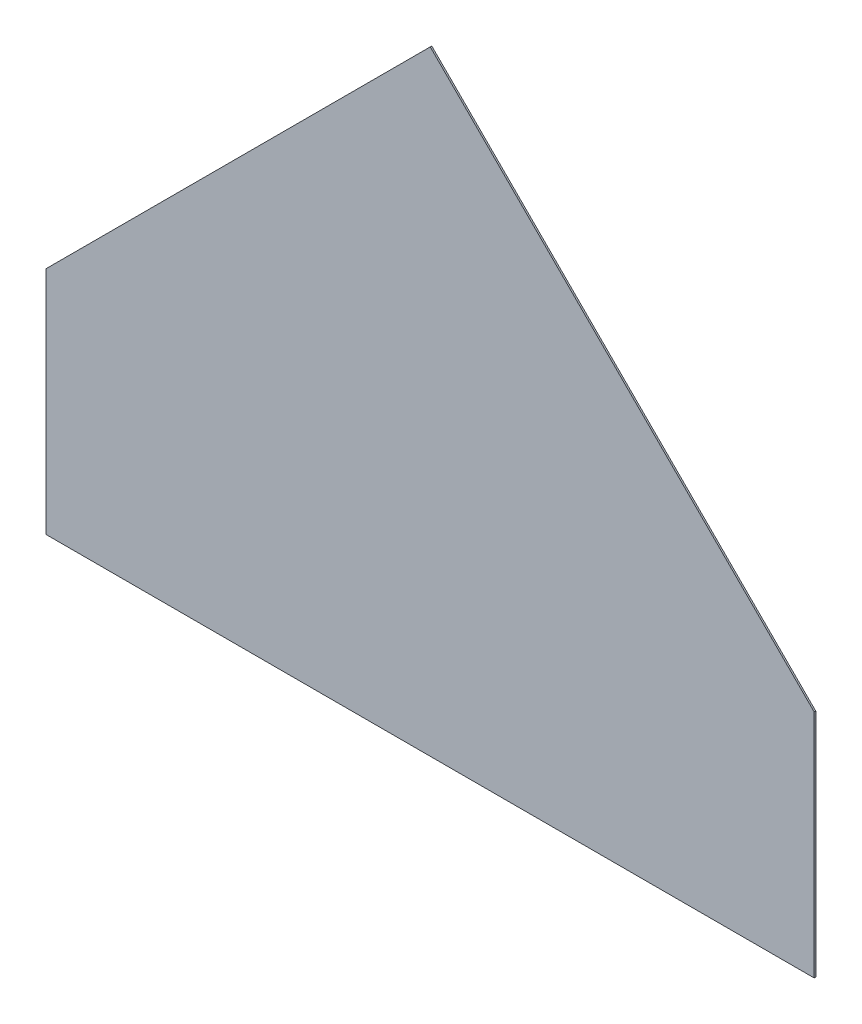
SolidWorks part; units mm, degrees
ref_plane "Front Plane" through (0, 0, 0) normal (0, 0, 1) x (1, 0, 0)
ref_plane "Top Plane" through (0, 0, 0) normal (0, 1, 0) x (1, 0, 0)
ref_plane "Right Plane" through (0, 0, 0) normal (1, 0, 0) x (0, 0, -1)
sketch "Sketch1" plane through (0, 0, 0) normal (0, 0, 1) x (1, 0, 0)
  line L0 (0, 42.8622) -> (0, -57.5859) construction
  line L1 (0, 0) -> (-25, 0)
  line L2 (0, 0) -> (25, 0)
  line L3 (-25, 0) -> (-25, 15)
  line L4 (-25, 15) -> (-3.7868, 36.2132)
  line L5 (-3.7868, 36.2132) -> (0, 40)
  line L6 (25, 0) -> (25, 15)
  line L7 (25, 15) -> (0, 40)
  dimension "D1" = 45
extrude "Boss-Extrude1" add sketch "Sketch1" along normal blind 0.1
